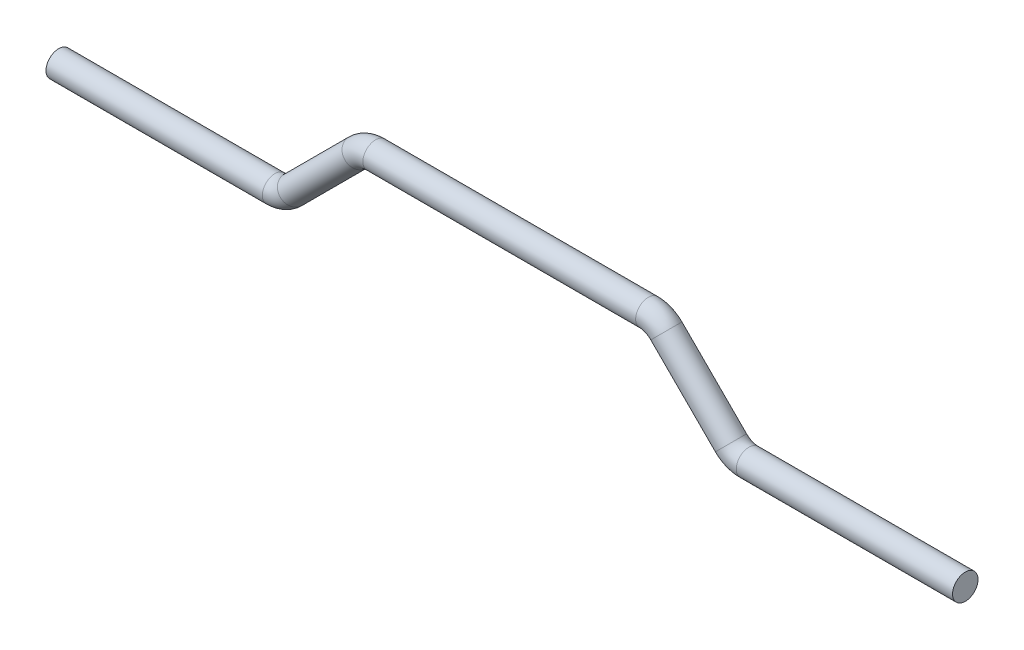
SolidWorks part; units mm, degrees
ref_plane "Plane1" through (0, 0, 0) normal (0, 0, 1) x (1, 0, 0)
ref_plane "Plane2" through (0, 0, 0) normal (0, 1, 0) x (1, 0, 0)
ref_plane "Plane3" through (0, 0, 0) normal (1, 0, 0) x (0, 0, -1)
sketch "Sketch1" plane through (0, 0, 0) normal (0, 0, 1) x (1, 0, 0)
  line L0 (0, 0) -> (0, 58) construction
  line L1 (42.8726, 0) -> (-42.8726, 0)
  line L2 (-48.5294, -2.3431) -> (-68.8431, -22.6569)
  line L3 (48.5294, -2.3431) -> (68.8431, -22.6569)
  line L4 (-74.5, -25) -> (-142.5, -25)
  line L5 (74.5, -25) -> (142.5, -25)
  arc A0 (-42.8726, 0) -> (-48.5294, -2.3431) centre (-42.8726, -8) ccw
  arc A1 (42.8726, 0) -> (48.5294, -2.3431) centre (42.8726, -8) cw
  arc A2 (-68.8431, -22.6569) -> (-74.5, -25) centre (-74.5, -17) cw
  arc A3 (68.8431, -22.6569) -> (74.5, -25) centre (74.5, -17) ccw
  dimension "D2" = 8
  dimension "D6" = 8
  dimension "D1" = 68
  dimension "D3" = 285
  dimension "D4" = 45
  dimension "D5" = 25
ref_plane "Plane4" through (-142.5, -25, 0) normal (-1, 0, 0) x (0, 0, 1)
sketch "Sketch2" plane through (-142.5, -25, 0) normal (-1, 0, 0) x (0, 0, 1)
  circle A0 centre (0, 0) radius 4
  dimension "D1" = 8
sweep "Base-Sweep" add profiles "Sketch2" path "Sketch1"
